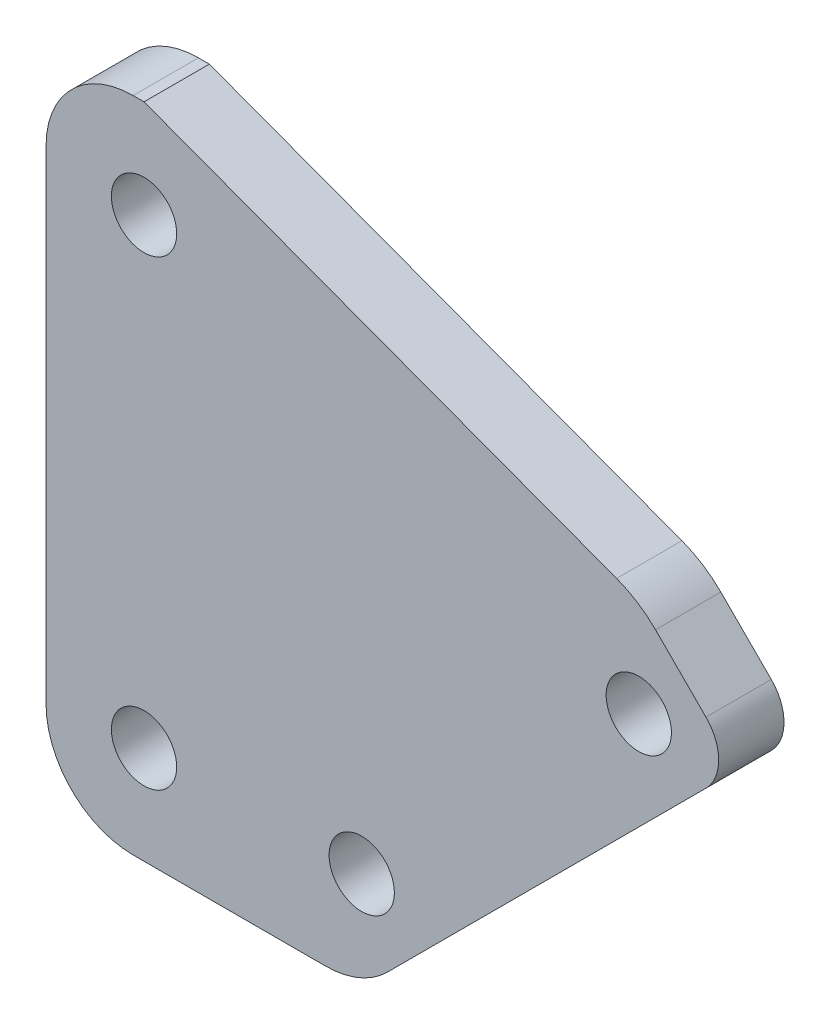
SolidWorks part; units mm, degrees
ref_plane "Front Plane" through (0, 0, 0) normal (0, 0, 1) x (1, 0, 0)
ref_plane "Top Plane" through (0, 0, 0) normal (0, 1, 0) x (1, 0, 0)
ref_plane "Right Plane" through (0, 0, 0) normal (1, 0, 0) x (0, 0, -1)
sketch "Sketch1" plane through (0, 0, 0) normal (0, 0, 1) x (1, 0, 0)
  line L0 (0, 15.1066) -> (33.9713, 15.1066) construction
  line L1 (0, 0) -> (14.5, 0)
  line L2 (0, 0) -> (0, 30.2132)
  line L3 (0, 30.2132) -> (4.5, 30.2132)
  line L5 (16.9856, 0) -> (16.9856, 27) construction
  line L6 (4.5, 6) -> (4.5, 24.2132) construction
  line L7 (4.5, 3) -> (4.5, 0) construction
  line L8 (3, 4.5) -> (0, 4.5) construction
  line L9 (4.5, 27.2132) -> (4.5, 30.2132) construction
  line L10 (3, 25.7132) -> (0, 25.7132) construction
  line L11 (6, 4.5) -> (13, 4.5) construction
  line L12 (14.5, 6) -> (14.5, 3) construction
  line L13 (13, 4.5) -> (16, 4.5) construction
  line L14 (14.5, 4.5) -> (15.5607, 5.5607) construction
  line L15 (14.5, 4.5) -> (32.8614, 22.8614) construction
  line L16 (15.5607, 5.5607) -> (26.1673, 16.1673) construction
  line L17 (27.2279, 18.7279) -> (27.2279, 21.7279) construction
  line L18 (28.7279, 17.2279) -> (31.7279, 17.2279)
  line L19 (4.5, 30.2132) -> (27.2279, 21.7279)
  line L20 (27.2279, 21.7279) -> (31.7279, 17.2279)
  line L21 (16, 4.5) -> (19, 4.5)
  line L22 (19, 4.5) -> (31.7279, 17.2279)
  line L23 (19, 4.5) -> (14.5, 0)
  line L24 (25.364, 10.864) -> (7.9636, 28.2643) construction
  line L25 (4.5, 25.7132) -> (7.5074, 28.7206) construction
  line L26 (7.5074, 28.7206) -> (-7.8075, 13.4057) construction
  line L27 (4.5, 4.5) -> (-6.1066, 15.1066) construction
  circle A0 centre (4.5, 25.7132) radius 1.5
  circle A1 centre (4.5, 4.5) radius 1.5
  circle A2 centre (14.5, 4.5) radius 1.5
  circle A3 centre (27.2279, 17.2279) radius 1.5
  dimension "D1" = 3
  dimension "D2" = 3
  dimension "D8" = 3
  dimension "D10" = 3
  dimension "D3" = 15
  dimension "D4" = 3
  dimension "D5" = 3
  dimension "D6" = 3
  dimension "D7" = 3
  dimension "D9" = 7
  dimension "D11" = 15
  dimension "D12" = 3
  dimension "D13" = 3
  dimension "D14" = 3
extrude "Boss-Extrude1" add sketch "Sketch1" along normal blind 3
fillet "Fillet1" radius 2 1 edges at (31.7279, 17.2279, 1.5)
fillet "Fillet3" radius 5 1 edges at (27.2279, 21.7279, 1.5)
fillet "Fillet5" radius 4 1 edges at (0, 30.2132, 1.5)
fillet "Fillet6" radius 4 1 edges at (0, 0, 1.5)
fillet "Fillet7" radius 4 1 edges at (14.5, 0, 1.5)
